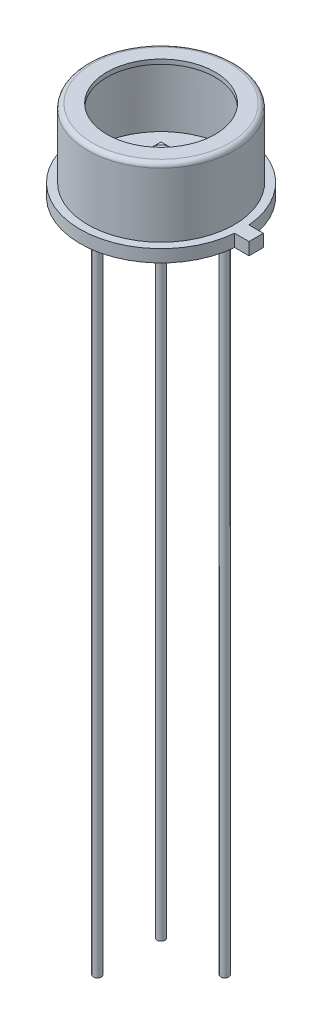
SolidWorks part; units mm, degrees
ref_plane "Front Plane" through (0, 0, 0) normal (0, 0, 1) x (1, 0, 0)
ref_plane "Top Plane" through (0, 0, 0) normal (0, 1, 0) x (1, 0, 0)
ref_plane "Right Plane" through (0, 0, 0) normal (1, 0, 0) x (0, 0, -1)
sketch "Sketch1" plane through (0, 0, 0) normal (0, 0, 1) x (1, 0, 0)
  line L0 (0, 0) -> (0, 37.7864) construction
  line L2 (4.572, 0) -> (4.572, 0.7)
  line L3 (4.572, 0.7) -> (4.13, 0.7)
  line L6 (4.13, 0.7) -> (4.13, 4.318)
  line L7 (3.876, 4.572) -> (3.05, 4.572)
  arc A0 (4.13, 4.318) -> (3.876, 4.572) centre (3.876, 4.318) ccw
  dimension "D7" = 0.254
  dimension "D1" = 0.7
  dimension "D2" = 8.26
  dimension "D4" = 9.144
  dimension "D6" = 4.572
  dimension "D8" = 6.1
revolve "Revolve-Thin2" add sketch "Sketch1" angle 360 about L0
sketch "Sketch2" plane through (0, 0, 0) normal (0, -1, 0) x (1, 0, 0)
  circle A1 centre (0, 0) radius 4.572
  circle A2 centre (0, 0) radius 4.572
  dimension "D1" = 0
extrude "Boss-Extrude1" add sketch "Sketch2" against normal up to surface (0.446 mm away) up to face at (0, 0.446, -3.876)
sketch "Sketch3" plane through (0, 0, 0) normal (0, -1, 0) x (1, 0, 0)
  line L0 (0.6, 0.6) -> (-0.6, -0.6) construction
  line L1 (-0.6, 0.6) -> (0.6, 0.6)
  line L2 (-0.6, 0.6) -> (-0.6, -0.6)
  line L3 (-0.6, -0.6) -> (0.6, -0.6)
  line L4 (0.6, 0.6) -> (0.6, -0.6)
  dimension "D1" = 1.2
extrude "Boss-Extrude2" add sketch "Sketch3" along normal blind 0.05 from offset 2.0792 separate body offset against normal yes
sketch "Sketch8" plane through (0, 2.0792, 0) normal (0, 1, 0) x (-1, 0, 0)
  circle A0 centre (0, 0) radius 0.51
  dimension "D1" = 1.02
extrude "Boss-Extrude6" add sketch "Sketch8" along normal blind 0.1
sketch "Sketch5" plane through (0, 0, 0) normal (0, -1, 0) x (1, 0, 0)
  line L0 (0, 0) -> (-1.7961, 1.7961) construction
  line L1 (0, 0) -> (1.7961, -1.7961) construction
  line L2 (0, 0) -> (-1.7961, -1.7961) construction
  circle A0 centre (0, 0) radius 2.54 construction
  circle A1 centre (-1.7961, -1.7961) radius 0.225
  circle A2 centre (1.7961, -1.7961) radius 0.225
  circle A3 centre (-1.7961, 1.7961) radius 0.225
  circle A4 centre (0, 0) radius 4.572 construction
  dimension "D1" = 5.08
  dimension "D2" = 0.45
extrude "Boss-Extrude4" add sketch "Sketch5" along normal blind 38
sketch "Sketch7" plane through (0, 0, 0) normal (0, -1, 0) x (1, 0, 0)
  circle A0 centre (-1.7961, 1.7961) radius 0.275
  dimension "D1" = 0.55
extrude "Boss-Extrude5" [suppressed] add sketch "Sketch7" along normal blind 0.2
sketch "Sketch10" plane through (0, 0, 0) normal (0, -1, 0) x (1, 0, 0)
  line L0 (0, 0) -> (5.364, 0) construction
  line L2 (5.364, -0.405) -> (4.554, -0.405)
  line L3 (5.364, -0.405) -> (5.364, 0.405)
  line L4 (5.364, 0.405) -> (4.554, 0.405)
  line L5 (4.554, -0.405) -> (4.554, 0.405)
  line L6 (5.364, -0.405) -> (4.554, 0.405) construction
  line L7 (5.364, 0.405) -> (4.554, -0.405) construction
  circle A0 centre (0, 0) radius 4.572 construction
  point P6 (4.959, 0)
  dimension "D1" = 0.81
  dimension "D2" = 0.81
extrude "Boss-Extrude7" add sketch "Sketch10" against normal blind 0.7
sketch "Sketch12" plane through (0, 0, 0) normal (0, -1, 0) x (1, 0, 0)
  circle A0 centre (0, 0) radius 2.54 construction
